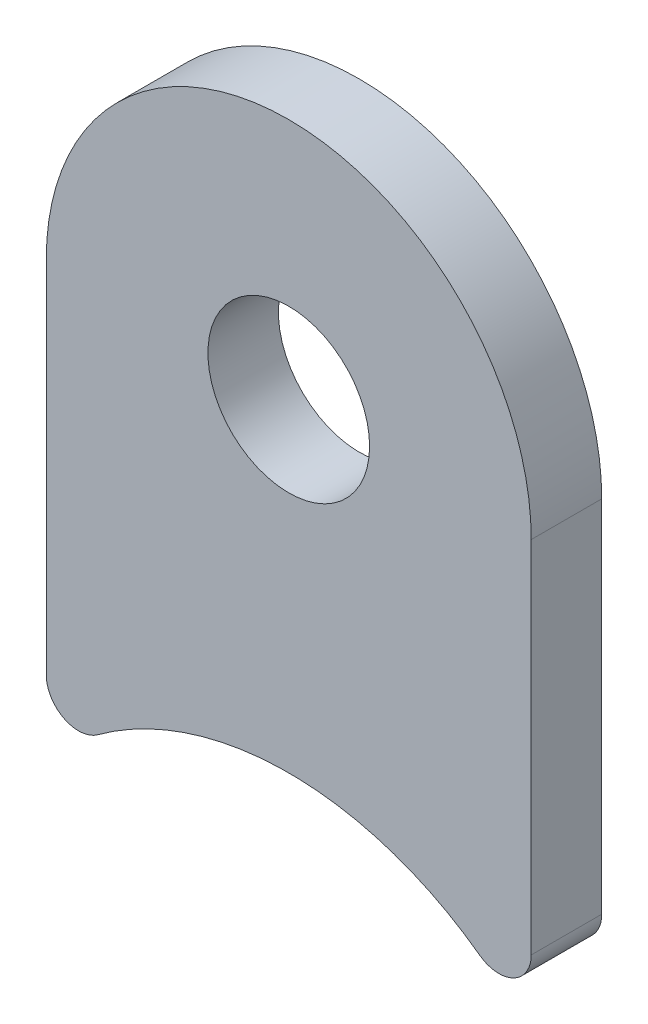
SolidWorks part; units mm, degrees
material "Plain Carbon Steel"
ref_plane "Front" through (0, 0, 0) normal (0, 0, 1) x (1, 0, 0)
ref_plane "Top" through (0, 0, 0) normal (0, 1, 0) x (1, 0, 0)
ref_plane "Right" through (0, 0, 0) normal (1, 0, 0) x (0, 0, -1)
sketch "Sketch1" plane through (0, 0, 0) normal (0, 0, 1) x (1, 0, 0)
  line L0 (9.525, 11.2701) -> (9.525, 25.4)
  line L1 (-9.525, 25.4) -> (-9.525, 11.2701)
  line L2 (0, 0) -> (0, 25.4) construction
  arc A0 (7.5045, 10.2456) -> (-7.5045, 10.2456) centre (0, 0) ccw
  circle A1 centre (0, 25.4) radius 3.175
  arc A2 (9.525, 25.4) -> (-9.525, 25.4) centre (0, 25.4) ccw
  arc A3 (9.525, 11.2701) -> (7.5045, 10.2456) centre (8.255, 11.2701) cw
  arc A4 (-9.525, 11.2701) -> (-7.5045, 10.2456) centre (-8.255, 11.2701) ccw
  point P10 (12.7, 0)
  point P13 (-12.7, 0)
  dimension "D1" = 12.7
  dimension "D2" = 6.35
  dimension "D4" = 1.27
  dimension "D5" = 9.525
  dimension "D3" = 25.4
extrude "Boss-Extrude1" add sketch "Sketch1" along normal mid plane 2.7686
